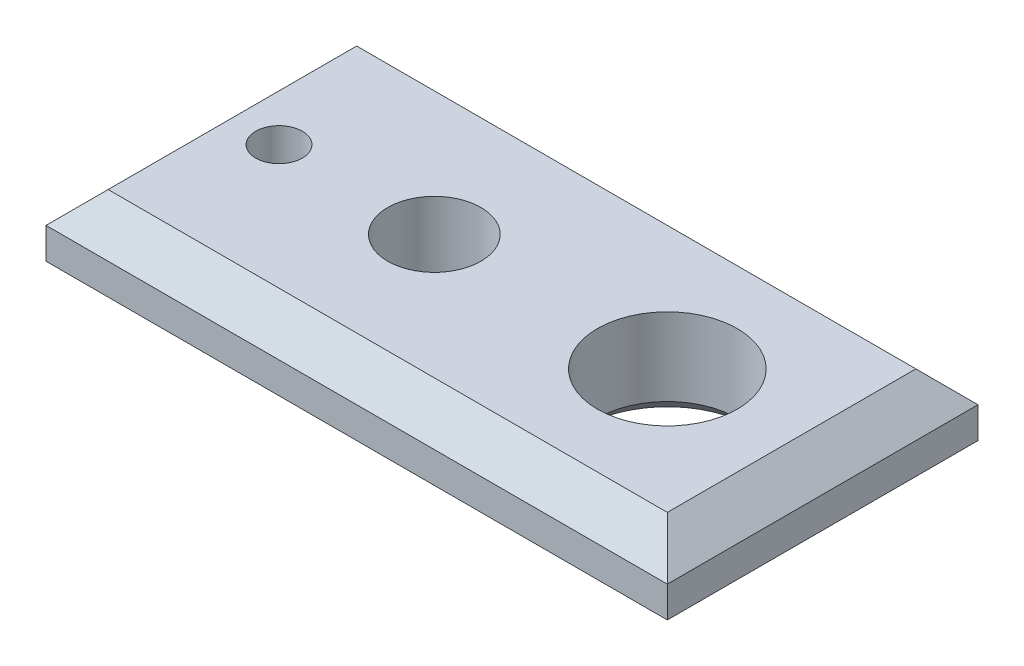
SolidWorks part; units mm, degrees
ref_plane "Alzado" through (0, 0, 0) normal (0, 0, 1) x (1, 0, 0)
ref_plane "Planta" through (0, 0, 0) normal (0, 1, 0) x (1, 0, 0)
ref_plane "Vista lateral" through (0, 0, 0) normal (1, 0, 0) x (0, 0, -1)
sketch "Croquis1" plane through (0, 0, 0) normal (0, 1, 0) x (1, 0, 0)
  line L1 (-100, 50) -> (100, 50)
  line L2 (-100, 50) -> (-100, -50)
  line L3 (-100, -50) -> (100, -50)
  line L4 (100, 50) -> (100, -50)
  line L5 (-100, 50) -> (100, -50) construction
  line L6 (-100, -50) -> (100, 50) construction
  point P0 (0, 0)
  dimension "D1" = 200
  dimension "D2" = 100
extrude "Saliente-Extruir1" add sketch "Croquis1" along normal blind 10
ref_plane "Plano1" through (0, -10, 0) normal (0, 1, 0) x (1, 0, 0)
sketch "Croquis2" plane through (0, -10, 0) normal (0, 1, 0) x (1, 0, 0)
  line L0 (-100, 50) -> (-100, -50) construction
  line L1 (-90, 40) -> (90, 40)
  line L2 (-90, 40) -> (-90, -40)
  line L3 (-90, -40) -> (90, -40)
  line L4 (90, 40) -> (90, -40)
  line L5 (-90, 40) -> (90, -40) construction
  line L6 (-90, -40) -> (90, 40) construction
  line L7 (-100, -50) -> (100, -50) construction
  point P0 (0, 0)
  dimension "D1" = 10
  dimension "D2" = 10
loft "Recubrir1" add profiles "Croquis2" section "Croquis2" section face at (0, 0, 0)
ref_plane "Plano2" through (0, 20, 0) normal (0, 1, 0) x (1, 0, 0)
sketch "Croquis3" plane through (0, 20, 0) normal (0, 1, 0) x (1, 0, 0)
  line L0 (-100, 50) -> (-100, -50) construction
  line L1 (-90, 40) -> (90, 40)
  line L2 (-90, 40) -> (-90, -40)
  line L3 (-90, -40) -> (90, -40)
  line L4 (90, 40) -> (90, -40)
  line L5 (-90, 40) -> (90, -40) construction
  line L6 (-90, -40) -> (90, 40) construction
  line L7 (-100, -50) -> (100, -50) construction
  point P0 (0, 0)
  dimension "D1" = 10
  dimension "D2" = 10
loft "Recubrir2" add profiles "Croquis3" section "Croquis3" section face at (0, 10, 0)
sketch "Croquis4" plane through (0, 20, 0) normal (0, 1, 0) x (1, 0, 0)
  line L0 (-100, 50) -> (-100, -50) construction
  line L1 (-100, 0) -> (-75, 0) construction
  line L2 (-75, 0) -> (-25, 0) construction
  line L3 (-25, 0) -> (50, 0) construction
  circle A0 centre (-75, 0) radius 7.5
  circle A1 centre (-25, 0) radius 15
  circle A2 centre (50, 0) radius 22.5
  dimension "D2" = 15
  dimension "D4" = 30
  dimension "D6" = 45
  dimension "D1" = 25
  dimension "D3" = 50
  dimension "D5" = 75
extrude "Cortar-Extruir1" cut sketch "Croquis4" against normal blind 30
chamfer "Chaflán2" distance 5 angle 45 3 edges at (50, -10, 22.5) (-25, -10, 15) (-75, -10, 7.5)
